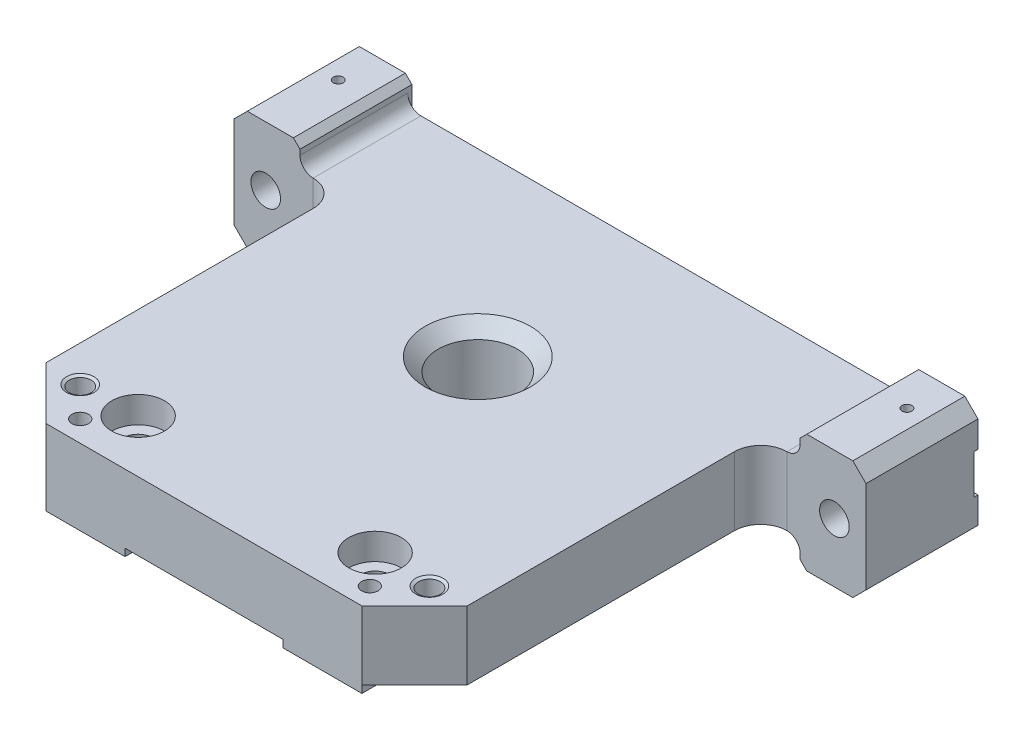
SolidWorks part; units mm, degrees
material "6061-T6 Al"
ref_plane "Front" through (0, 0, 0) normal (0, 0, 1) x (1, 0, 0)
ref_plane "Top" through (0, 0, 0) normal (0, 1, 0) x (1, 0, 0)
ref_plane "Right" through (0, 0, 0) normal (1, 0, 0) x (0, 0, -1)
sketch "Sketch1" plane through (0, 0, 0) normal (0, 0, 1) x (1, 0, 0)
  line L0 (76.2, 27.94) -> (76.2, 44.45)
  line L2 (76.2, 44.45) -> (-76.2, 44.45)
  line L4 (-76.2, 44.45) -> (-76.2, 27.94)
  line L8 (-76.2, 27.94) -> (76.2, 27.94)
  dimension "D1" = 76.2
  dimension "D2" = 27.94
  dimension "D3" = 76.2
  dimension "D5" = 16.51
extrude "Extrude1" add sketch "Sketch1" along normal blind 11.1252
sketch "Sketch2" plane through (0, 0, 11.1252) normal (0, 0, 1) x (1, 0, 0)
  line L0 (50.8, 27.94) -> (50.8, 44.45)
  line L1 (-76.2, 27.94) -> (76.2, 27.94) construction
  line L2 (76.2, 44.45) -> (-76.2, 44.45) construction
  line L3 (50.8, 44.45) -> (-50.8, 44.45)
  line L7 (-50.8, 44.45) -> (-50.8, 27.94)
  line L11 (-50.8, 27.94) -> (50.8, 27.94)
  line L12 (76.2, 27.94) -> (76.2, 44.45) construction
  line L14 (-76.2, 44.45) -> (-76.2, 27.94) construction
  dimension "D1" = 25.4
  dimension "D2" = 25.4
extrude "Extrude2" add sketch "Sketch2" along normal blind 99.3648
sketch "Sketch4" plane through (0, 27.94, 0) normal (0, -1, 0) x (1, 0, 0)
  line L1 (-38.1, 110.49) -> (-19.05, 110.49)
  line L2 (-38.1, 110.49) -> (-38.1, 91.44)
  line L3 (-38.1, 91.44) -> (-19.05, 91.44)
  line L4 (-19.05, 110.49) -> (-19.05, 91.44)
  line L7 (19.05, 110.49) -> (38.1, 110.49)
  line L8 (19.05, 110.49) -> (19.05, 91.44)
  line L9 (19.05, 91.44) -> (38.1, 91.44)
  line L10 (38.1, 110.49) -> (38.1, 91.44)
  dimension "D1" = 19.05
  dimension "D2" = 38.1
  dimension "D3" = 19.05
  dimension "D4" = 19.05
  dimension "D5" = 19.05
  dimension "D6" = 91.44
extrude "Extrude4" add sketch "Sketch4" along normal blind 2.54
sketch "Sketch23" plane through (0, 44.45, 0) normal (0, 1, 0) x (1, 0, 0)
  line L0 (76.2, -11.1252) -> (76.2, 0) construction
  line L1 (50.8, -11.1252) -> (76.2, -11.1252)
  line L2 (50.8, -11.1252) -> (50.8, -27.0129)
  line L3 (50.8, -27.0129) -> (76.2, -27.0129)
  line L4 (76.2, -11.1252) -> (76.2, -27.0129)
  line L5 (-76.2, -11.1252) -> (-76.2, 0) construction
  line L6 (-50.8, -11.1252) -> (-76.2, -11.1252)
  line L7 (-50.8, -11.1252) -> (-50.8, -27.0129)
  line L8 (-50.8, -27.0129) -> (-76.2, -27.0129)
  line L9 (-76.2, -11.1252) -> (-76.2, -27.0129)
  dimension "D1" = 15.8877
extrude "Extrude17" add sketch "Sketch23" against normal up to surface (16.51 mm away) up to face at (-3.5719, 27.94, 73.2853)
sketch "Sketch45" plane through (0, 0, 0) normal (0, 0, -1) x (-1, 0, 0)
  line L1 (-76.2, 44.45) -> (-60.325, 44.45)
  line L2 (-76.2, 44.45) -> (-76.2, 50.4825)
  line L3 (-76.2, 50.4825) -> (-60.325, 50.4825)
  line L4 (-60.325, 44.45) -> (-60.325, 50.4825)
  line L5 (-76.2, 27.94) -> (-60.325, 27.94)
  line L6 (-76.2, 27.94) -> (-76.2, 21.9075)
  line L7 (-76.2, 21.9075) -> (-60.325, 21.9075)
  line L8 (-60.325, 27.94) -> (-60.325, 21.9075)
  line L9 (76.2, 44.45) -> (60.325, 44.45)
  line L10 (76.2, 44.45) -> (76.2, 50.4825)
  line L11 (76.2, 50.4825) -> (60.325, 50.4825)
  line L12 (60.325, 44.45) -> (60.325, 50.4825)
  line L13 (76.2, 27.94) -> (60.325, 27.94)
  line L14 (76.2, 27.94) -> (76.2, 21.9075)
  line L15 (76.2, 21.9075) -> (60.325, 21.9075)
  line L16 (60.325, 27.94) -> (60.325, 21.9075)
  dimension "D1" = 28.575
  dimension "D2" = 15.875
extrude "Extrude20" add sketch "Sketch45" against normal up to surface (27.0129 mm away) up to face at (63.5, 36.195, 27.0129)
sketch "Sketch46" plane through (0, 0, 0) normal (0, 0, -1) x (-1, 0, 0)
  line L1 (-60.325, 44.45) -> (60.325, 44.45)
  line L2 (-60.325, 44.45) -> (-60.325, 40.9575)
  line L3 (-60.325, 27.94) -> (60.325, 27.94)
  line L4 (-60.325, 40.9575) -> (-76.2, 40.9575)
  line L6 (60.325, 27.94) -> (-60.325, 27.94) construction
  line L7 (-60.325, 44.45) -> (60.325, 44.45) construction
  line L8 (-76.2, 21.9075) -> (-76.2, 50.4825) construction
  line L9 (-76.2, 40.9575) -> (-76.2, 31.4325)
  line L10 (-76.2, 31.4325) -> (-60.325, 31.4325)
  line L11 (-60.325, 31.4325) -> (-60.325, 27.94)
  line L12 (60.325, 44.45) -> (60.325, 40.9575)
  line L13 (60.325, 40.9575) -> (76.2, 40.9575)
  line L14 (76.2, 50.4825) -> (76.2, 21.9075) construction
  line L15 (76.2, 40.9575) -> (76.2, 31.4325)
  line L16 (76.2, 31.4325) -> (60.325, 31.4325)
  line L17 (60.325, 31.4325) -> (60.325, 27.94)
  dimension "D1" = 9.525
extrude "Extrude21" cut sketch "Sketch46" against normal blind 1.016
fillet "Fillet3" radius 3.175 4 edges at (-60.325, 44.45, 14.0145) (-60.325, 27.94, 14.0144) (60.325, 27.94, 14.0145)
hole_wizard "1/4 Clearance Hole1" positions "Sketch10" profile "Sketch9" hole size "1/4" standard "Ansi Inch" end condition through all
sketch "Sketch10" plane through (56.8158, 10.0849, 27.0129) normal (0, 0, 1) x (1, 0, 0)
  line L0 (19.3842, 11.8226) -> (19.3842, 40.3976) construction
  point P1 (-125.3958, 26.1101)
  point P3 (11.7642, 26.1101)
  point P14 (19.3842, 26.1101)
  dimension "D1" = 137.16
  dimension "D2" = 68.58
sketch "Sketch9" plane through (-68.58, 36.195, 27.0129) normal (1, 0, 0) x (0, -1, 0)
  line L0 (0, 0) -> (0, 27.0129)
  line L1 (0, 27.0129) -> (3.5712, 27.0129)
  line L2 (3.5712, 27.0129) -> (3.5712, 0)
  line L5 (3.5712, 0) -> (0, 0)
  line L11 (0, -6.35) -> (0, 107.95) construction
  dimension "Thru Hole Dia." = 7.1425
  dimension "Thru Hole Depth" = 27.0129
hole_wizard "3/4 (0.75) Diameter Hole1" positions "Sketch31" profile "Sketch30" hole size "3/4" standard "Ansi Inch" end condition through all
sketch "Sketch31" plane through (0, 44.45, 0) normal (0, 1, 0) x (-1, 0, 0)
  point P0 (0, 44.45)
  dimension "D1" = 44.45
sketch "Sketch30" plane through (0, 44.45, 44.45) normal (1, 0, 0) x (0, 0, 1)
  line L0 (0, 0) -> (0, 22.5425)
  line L1 (0, 22.5425) -> (10.16, 22.5425)
  line L2 (9.525, 21.9075) -> (9.525, 3.175)
  line L3 (9.525, 3.175) -> (12.7, 0)
  line L5 (12.7, 0) -> (0, 0)
  line L6 (-9.525, 3.175) -> (-12.7, 0) construction
  line L7 (10.16, 22.5425) -> (9.525, 21.9075)
  line L8 (-10.16, 22.5425) -> (-9.525, 21.9075) construction
  line L11 (0, -6.35) -> (0, 107.95) construction
  dimension "Thru Hole Dia." = 19.05
  dimension "Thru Hole Depth" = 22.5425
  dimension "Near C'Sink Dia." = 25.4
  dimension "Near C'Sink Angle" = 90
  dimension "Far C'Sink Dia." = 20.32
  dimension "Far C'Sink Angle" = 90
hole_wizard "CBORE for  Socket Head Cap Screw0" positions "Sketch8" profile "Sketch7" counterbore size "1/4" standard "Ansi Inch" end condition up to next
sketch "Sketch8" plane through (0, 44.45, 0) normal (0, 1, 0) x (-1, 0, 0)
  point P0 (28.575, 97.79)
  point P1 (-28.575, 97.79)
  dimension "D1" = 57.15
  dimension "D2" = 97.79
  dimension "D3" = 28.575
sketch "Sketch7" plane through (-28.575, 44.45, 97.79) normal (1, 0, 0) x (0, 0, 1)
  line L0 (0, 0) -> (0, 19.05)
  line L1 (3.5712, 18.5572) -> (4.064, 19.05)
  line L2 (3.5712, 18.5572) -> (3.5712, 6.35)
  line L3 (3.5712, 6.35) -> (6.35, 6.35)
  line L4 (6.35, 6.35) -> (6.35, 0)
  line L5 (6.35, 0) -> (0, 0)
  line L11 (0, -6.35) -> (0, 107.95) construction
  line L12 (4.064, 19.05) -> (0, 19.05)
  line L13 (-3.5712, 18.5572) -> (-4.064, 19.05) construction
  dimension "Thru Hole Dia." = 7.1425
  dimension "Thru Hole Depth" = 19.05
  dimension "C'Bore Dia." = 12.7
  dimension "C'Bore Depth" = 6.35
  dimension "Far C'Sink Dia." = 8.128
  dimension "Far C'Sink Angle" = 90
hole_wizard "1/8\" Press Pin Holes" positions "Sketch48" profile "Sketch47" counterbore size "#6" standard "Ansi Inch"
sketch "Sketch48" plane through (0, 0, 0) normal (0, 0, -1) x (-1, 0, 0)
  circle A0 centre (68.58, 36.195) radius 3.5712 construction
  point P0 (-68.58, 45.72)
  point P1 (68.58, 45.72)
  dimension "D3" = 9.525
  dimension "D1" = 68.58
  dimension "D2" = 137.16
sketch "Sketch47" plane through (68.58, 45.72, 0) normal (1, 0, 0) x (0, 1, 0)
  line L0 (0, 0) -> (0, 7.3039)
  line L1 (0, 7.3039) -> (1.5875, 6.35)
  line L2 (1.5875, 6.35) -> (1.5875, 1.524)
  line L3 (1.5875, 1.524) -> (1.6002, 1.524)
  line L5 (1.6002, 1.524) -> (1.6002, 0.3048)
  line L6 (1.6002, 0.3048) -> (1.905, 0)
  line L7 (1.905, 0) -> (0, 0)
  line L8 (-1.6002, 0.3048) -> (-1.905, 0) construction
  line L10 (0, 7.3039) -> (-1.5875, 6.35) construction
  line L11 (0, -6.35) -> (0, 107.95) construction
  dimension "Hole Dia." = 3.175
  dimension "Hole Depth" = 6.35
  dimension "C'Bore Dia." = 3.2004
  dimension "C'Bore Depth" = 1.524
  dimension "Near C'Sink Dia." = 3.81
  dimension "Near C'Sink Angle" = 90
  dimension "Drill Angle" = 118
hole_wizard "3/32 (0.09375) Diameter Hole1" positions "Sketch50" profile "Sketch49" hole size "3/32" standard "Ansi Inch"
sketch "Sketch50" plane through (0, 0, 0) normal (0, 0, -1) x (-1, 0, 0)
  point P0 (-68.58, 45.72)
  point P1 (68.58, 45.72)
sketch "Sketch49" plane through (68.58, 45.72, 0) normal (1, 0, 0) x (0, 1, 0)
  line L0 (0, 0) -> (0, 13.4154)
  line L1 (0, 13.4154) -> (1.1906, 12.7)
  line L2 (1.1906, 12.7) -> (1.1906, 0)
  line L5 (1.1906, 0) -> (0, 0)
  line L10 (0, 13.4154) -> (-1.1906, 12.7) construction
  line L11 (0, -6.35) -> (0, 107.95) construction
  dimension "Hole Dia." = 2.3812
  dimension "Hole Depth" = 12.7
  dimension "Drill Angle" = 118
hole_wizard "3/32 (0.09375) Diameter Hole2" positions "Sketch52" profile "Sketch51" hole size "3/32" standard "Ansi Inch"
sketch "Sketch52" plane through (0, 50.4825, 0) normal (0, 1, 0) x (-1, 0, 0)
  line L0 (-60.325, 0) -> (-76.2, 0) construction
  point P0 (-68.58, 9.525)
  point P1 (68.58, 9.525)
  dimension "D1" = 9.525
sketch "Sketch51" plane through (68.58, 50.4825, 9.525) normal (1, 0, 0) x (0, 0, 1)
  line L0 (0, 0) -> (0, 4.9064)
  line L1 (0, 4.9064) -> (1.1906, 4.191)
  line L2 (1.1906, 4.191) -> (1.1906, 0)
  line L5 (1.1906, 0) -> (0, 0)
  line L10 (0, 4.9064) -> (-1.1906, 4.191) construction
  line L11 (0, -6.35) -> (0, 107.95) construction
  dimension "Hole Dia." = 2.3812
  dimension "Hole Depth" = 4.191
  dimension "Drill Angle" = 118
fillet "Fillet4" radius 6.35 2 edges at (50.8, 36.195, 27.0129) (-50.8, 36.195, 27.0129)
chamfer "Chamfer6" distance 3.175 angle 45 4 edges at (-76.2, 21.9075, 13.5064) (-76.2, 50.4825, 13.5064) (76.2, 21.9075, 13.5064) (76.2, 50.4825, 13.5064)
chamfer "Chamfer7" distance 12.7 angle 45 2 edges at (50.8, 36.195, 110.49) (-50.8, 36.195, 110.49)
chamfer "Chamfer8" distance 1.5875 angle 45 4 edges at (-60.325, 21.9075, 13.5064) (60.325, 21.9075, 13.5064) (60.325, 50.4825, 13.5064) (-60.325, 50.4825, 13.5064)
chamfer "Chamfer9" distance 0.762 angle 45 8 edges at (28.575, 25.4, 91.44) (38.1, 25.4, 100.965) (28.575, 25.4, 110.49) (19.05, 25.4, 100.965) (-19.05, 25.4, 100.965) (-28.575, 25.4, 91.44) (-38.1, 25.4, 100.965) (-28.575, 25.4, 110.49)
hole_wizard "CBORE for #6 Socket Head Cap Screw2" positions "Sketch54" profile "Sketch53" counterbore size "#6" standard "Ansi Inch" end condition up to next
sketch "Sketch54" plane through (0, 44.45, 0) normal (0, 1, 0) x (-1, 0, 0)
  line L0 (-34.925, 105.41) -> (34.925, 105.41) construction
  line L3 (0, 15.7163) -> (0, -15.7163) construction
  line L4 (73.025, 0) -> (61.9125, 0) construction
  point P0 (34.925, 105.41)
  point P1 (-34.925, 105.41)
  point P9 (0, 105.41)
  dimension "D1" = 105.41
  dimension "D2" = 69.85
sketch "Sketch53" plane through (-34.925, 44.45, 105.41) normal (1, 0, 0) x (0, 0, 1)
  line L0 (0, 0) -> (0, 19.05)
  line L1 (1.6319, 18.7769) -> (1.905, 19.05)
  line L2 (1.6319, 18.7769) -> (1.6319, 12.7)
  line L3 (1.6319, 12.7) -> (1.9844, 12.7)
  line L4 (1.9844, 12.7) -> (1.9844, 0)
  line L5 (1.9844, 0) -> (0, 0)
  line L11 (0, -6.35) -> (0, 107.95) construction
  line L12 (1.905, 19.05) -> (0, 19.05)
  line L13 (-1.632, 18.7769) -> (-1.905, 19.05) construction
  dimension "Thru Hole Dia." = 3.2639
  dimension "Thru Hole Depth" = 19.05
  dimension "C'Bore Dia." = 3.9688
  dimension "C'Bore Depth" = 12.7
  dimension "Far C'Sink Dia." = 3.81
  dimension "Far C'Sink Angle" = 90
hole_wizard "Tapped Hole for #8-32 Helicoil2" positions "Sketch56" profile "Sketch55" tap size "#8-32" standard "Helicoil® Inch" end condition through all
sketch "Sketch56" plane through (0, 44.45, 0) normal (0, 1, 0) x (-1, 0, 0)
  line L0 (-42.1092, 98.2258) -> (-34.925, 105.41) construction
  line L3 (34.925, 105.41) -> (42.1092, 98.2258) construction
  line L6 (-34.925, 105.41) -> (34.925, 105.41) construction
  point P0 (42.1092, 98.2258)
  point P1 (-42.1092, 98.2258)
  dimension "D1" = 45
  dimension "D2" = 10.16
sketch "Sketch55" plane through (-42.1092, 44.45, 98.2258) normal (1, 0, 0) x (0, 0, 1)
  line L0 (0, 0) -> (0, 22.5425)
  line L1 (0, 22.5425) -> (2.1971, 22.5425)
  line L3 (2.1971, 22.5425) -> (2.1971, 10.3632)
  line L4 (2.6378, 10.3632) -> (2.1971, 10.3632)
  line L5 (2.6378, 10.3632) -> (2.6378, 0.3835)
  line L6 (2.6378, 0.3835) -> (3.302, 0)
  line L7 (3.302, 0) -> (0, 0)
  line L8 (-2.6378, 0.3835) -> (-3.302, 0) construction
  line L11 (0, -6.35) -> (0, 107.95) construction
  dimension "Thru Tap Drill Dia." = 4.3942
  dimension "Thru Tap Drill Depth" = 22.5425
  dimension "Thread Major Dia." = 5.2756
  dimension "Thread Depth" = 10.3632
  dimension "Near C'Sink Dia." = 6.604
  dimension "Near C'Sink Angle" = 120
